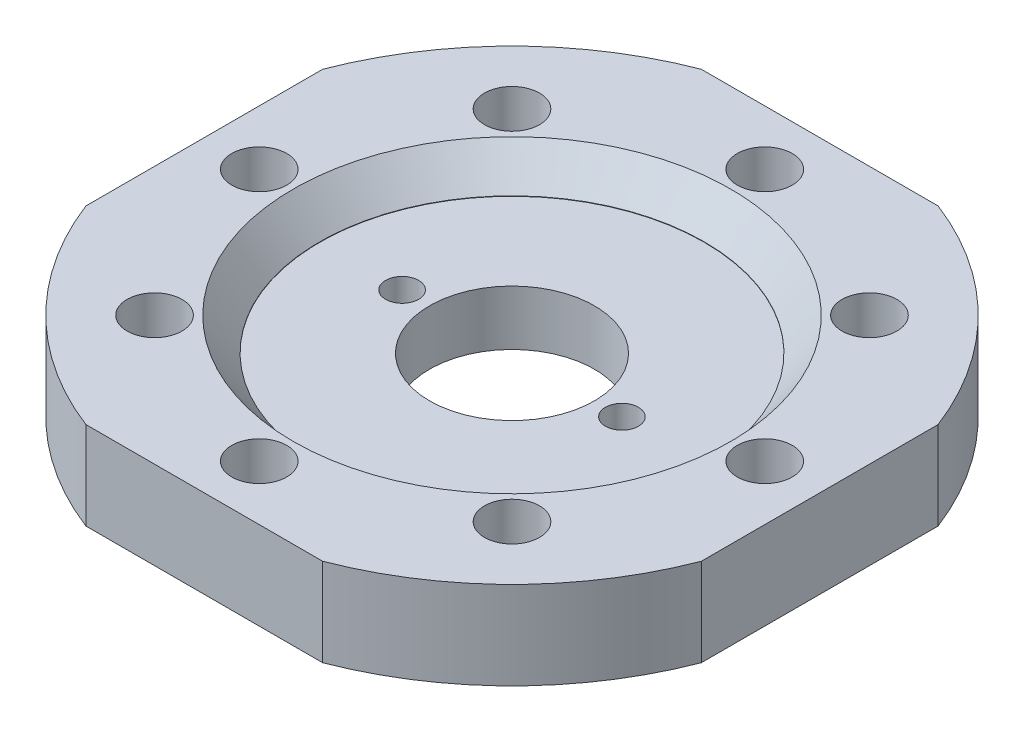
SolidWorks part; units mm, degrees
ref_plane "Front Plane" through (0, 0, 0) normal (0, 0, 1) x (1, 0, 0)
ref_plane "Top Plane" through (0, 0, 0) normal (0, 1, 0) x (1, 0, 0)
ref_plane "Right Plane" through (0, 0, 0) normal (1, 0, 0) x (0, 0, -1)
sketch "Sketch1" plane through (0, 0, 0) normal (0, 1, 0) x (1, 0, 0)
  circle A0 centre (0, 0) radius 150
  dimension "D1" = 300
extrude "Boss-Extrude1" add sketch "Sketch1" along normal blind 40
hole_wizard "CBORE for M64 Hex Head Bolt1" positions "Sketch2" profile "Sketch3" counterbore size "M64" standard "DIN" end condition through all
sketch "Sketch2" plane through (0, 40, 0) normal (0, 1, 0) x (1, 0, 0)
  point P0 (0, 0)
sketch "Sketch3" plane through (0, 40, 0) normal (1, 0, 0) x (0, 0, 1)
  line L0 (0, 0) -> (0, 40)
  line L1 (0, 40) -> (37.5, 40)
  line L3 (37.5, 40) -> (37.5, 15)
  line L4 (37.5, 15) -> (87.5, 15)
  line L5 (87.5, 15) -> (87.5, 0)
  line L7 (87.5, 0) -> (0, 0)
  line L11 (0, -6.35) -> (0, 107.95) construction
  dimension "Thru Hole Dia." = 75
  dimension "Thru Hole Depth" = 40
  dimension "C'Bore Dia." = 175
  dimension "C'Bore Depth" = 15
hole_wizard "Ø25.0 (25) Diameter Hole1" positions "Sketch4" profile "Sketch5" hole size "Ø25.0" standard "DIN" end condition through all
sketch "Sketch4" plane through (0, 40, 0) normal (0, 1, 0) x (1, 0, 0)
  line L0 (0, 0) -> (138.6313, 0) construction
  point P0 (115, 0)
  dimension "D1" = 115
sketch "Sketch5" plane through (115, 40, 0) normal (1, 0, 0) x (0, 0, 1)
  line L0 (0, 0) -> (0, 40)
  line L1 (0, 40) -> (12.5, 40)
  line L2 (12.5, 40) -> (12.5, 0)
  line L5 (12.5, 0) -> (0, 0)
  line L11 (0, -6.35) -> (0, 107.95) construction
  dimension "Thru Hole Dia." = 25
  dimension "Thru Hole Depth" = 40
pattern_circular "CirPattern2" count 8 over 360 about axis through (0, 0, 0) along (0, 1, 0) of "Ø25.0 (25) Diameter Hole1"
chamfer "Chamfer1" distance 12 angle 51 1 edges at (0, 40, 87.5)
ref_plane "Plane1" through (0, 0, 140) normal (0, 0, 1) x (1, 0, 0)
ref_plane "Plane2" through (0, 0, -140) normal (0, 0, 1) x (1, 0, 0)
ref_plane "Plane3" through (140, 0, 0) normal (1, 0, 0) x (0, 0, -1)
ref_plane "Plane4" through (-140, 0, 0) normal (1, 0, 0) x (0, 0, -1)
other "SurfaceCut1"
other "SurfaceCut2"
other "SurfaceCut3"
other "SurfaceCut4"
hole_wizard "Ø15.0 (15) Diameter Hole1" positions "Sketch6" profile "Sketch7" hole size "Ø15.0" standard "DIN"
sketch "Sketch6" plane through (0, 25, 0) normal (0, 1, 0) x (1, 0, 0)
  point P0 (-50, 0)
  point P2 (50, 0)
  dimension "D1" = 50
  dimension "D2" = 50
sketch "Sketch7" plane through (-50, 25, 0) normal (1, 0, 0) x (0, 0, 1)
  line L0 (0, 0) -> (0, 19.5065)
  line L1 (0, 19.5065) -> (7.5, 15)
  line L2 (7.5, 15) -> (7.5, 0)
  line L5 (7.5, 0) -> (0, 0)
  line L10 (0, 19.5065) -> (-7.5, 15) construction
  line L11 (0, -6.35) -> (0, 107.95) construction
  dimension "Hole Dia." = 15
  dimension "Hole Depth" = 15
  dimension "Drill Angle" = 118
